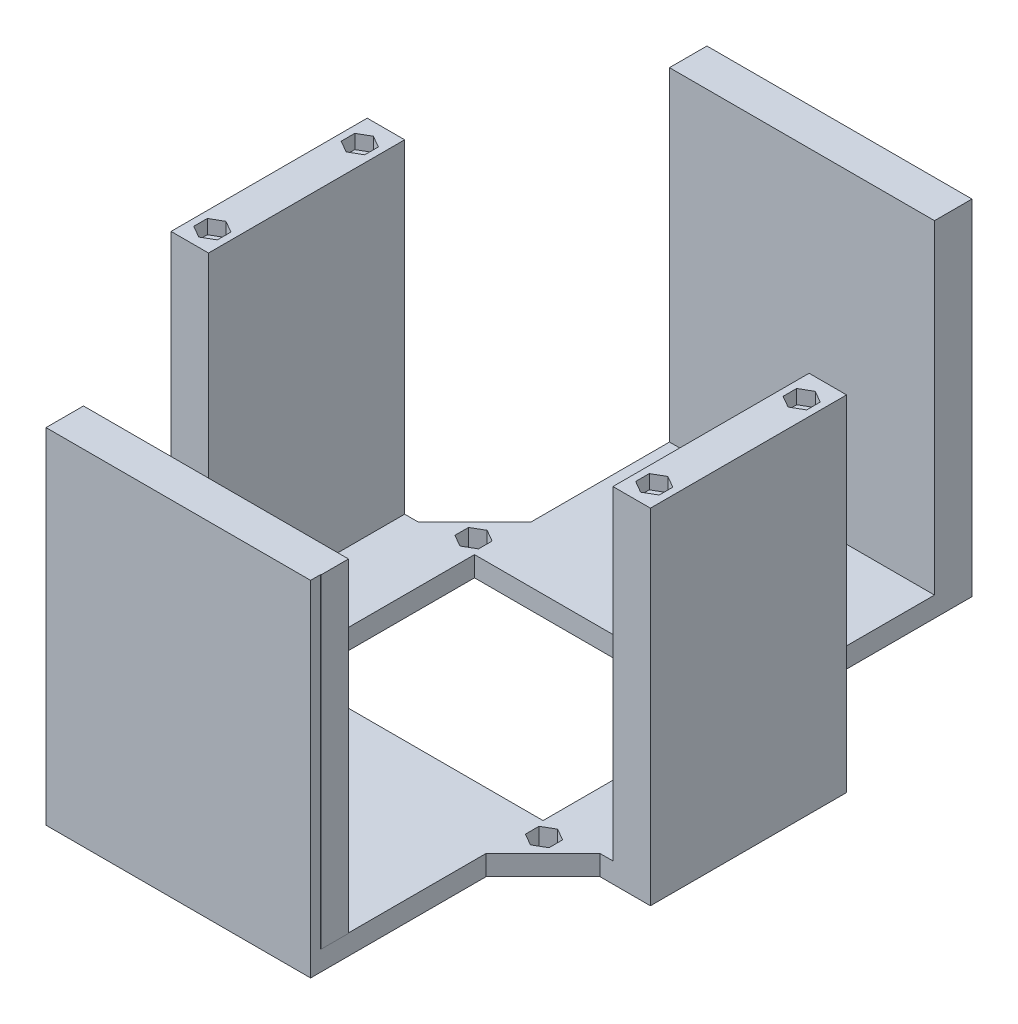
SolidWorks part; units mm, degrees
ref_plane "Front Plane" through (0, 0, 0) normal (0, 0, 1) x (1, 0, 0)
ref_plane "Top Plane" through (0, 0, 0) normal (0, 1, 0) x (1, 0, 0)
ref_plane "Right Plane" through (0, 0, 0) normal (1, 0, 0) x (0, 0, -1)
sketch "Sketch2" plane through (0, 0, 0) normal (0, 1, 0) x (1, 0, 0)
  line L0 (-32.8436, 36.3397) -> (-32.8436, 24.3397)
  line L1 (-32.8436, 24.3397) -> (-44.8436, 24.3397)
  line L2 (-44.8436, 24.3397) -> (-32.8436, 36.3397)
  line L3 (0, 57.5251) -> (0, -40.7887) construction
  line L4 (-92.2724, 0) -> (92.8059, 0) construction
  line L27 (32.8436, 24.3397) -> (44.8436, 24.3397)
  line L28 (32.8436, 36.3397) -> (32.8436, 24.3397)
  line L29 (44.8436, 24.3397) -> (32.8436, 36.3397)
  line L30 (44.8436, -24.3397) -> (32.8436, -36.3397)
  line L31 (32.8436, -36.3397) -> (32.8436, -24.3397)
  line L32 (32.8436, -24.3397) -> (44.8436, -24.3397)
  line L45 (-44.8436, -24.3397) -> (-32.8436, -36.3397)
  line L46 (-32.8436, -24.3397) -> (-44.8436, -24.3397)
  line L47 (-32.8436, -36.3397) -> (-32.8436, -24.3397)
  line L48 (39.425, -26.0613) -> (39.425, -29.4387)
  line L49 (-36.5, -31.1275) -> (-33.575, -29.4387)
  line L50 (-33.575, -29.4387) -> (-33.575, -26.0613)
  line L51 (-33.575, -26.0613) -> (-36.5, -24.3725)
  line L52 (-36.5, -24.3725) -> (-39.425, -26.0613)
  line L53 (-39.425, -26.0613) -> (-39.425, -29.4387)
  line L54 (-39.425, -29.4387) -> (-36.5, -31.1275)
  line L55 (39.425, -29.4387) -> (36.5, -31.1275)
  line L56 (36.5, -31.1275) -> (33.575, -29.4387)
  line L57 (33.575, -29.4387) -> (33.575, -26.0613)
  line L58 (33.575, -26.0613) -> (36.5, -24.3725)
  line L59 (36.5, -24.3725) -> (39.425, -26.0613)
  line L60 (33.575, 29.4387) -> (33.575, 26.0613)
  line L61 (36.5, 31.1275) -> (33.575, 29.4387)
  line L62 (39.425, 29.4387) -> (36.5, 31.1275)
  line L63 (39.425, 26.0613) -> (39.425, 29.4387)
  line L64 (36.5, 24.3725) -> (39.425, 26.0613)
  line L65 (33.575, 26.0613) -> (36.5, 24.3725)
  line L66 (-33.575, 29.4387) -> (-33.575, 26.0613)
  line L67 (-36.5, 31.1275) -> (-33.575, 29.4387)
  line L68 (-39.425, 29.4387) -> (-36.5, 31.1275)
  line L69 (-39.425, 26.0613) -> (-39.425, 29.4387)
  line L70 (-33.575, 26.0613) -> (-36.5, 24.3725)
  line L71 (-36.5, 24.3725) -> (-39.425, 26.0613)
  circle A7 centre (-36.5, -27.75) radius 2.925 construction
  point P0 (-36.5, 27.75)
  point P1 (-36.5, -27.75)
  point P2 (36.5, -27.75)
  point P3 (36.5, 27.75)
  point P43 (36.5, -27.75)
  point P55 (-36.5, -27.75)
  dimension "D6" = 12
  dimension "D2" = 73
  dimension "D3" = 55.5
  dimension "D8" = 73
  dimension "D9" = 55.5
  dimension "D10" = 27.75
  dimension "D11" = 5
  dimension "D12" = 36.5
  dimension "D13" = 36.5
  dimension "D5" = 12
  dimension "D14" = 27.75
  dimension "D15" = 27.75
  dimension "D16" = 5.85
extrude "Boss-Extrude1" add sketch "Sketch2" along normal blind 20
sketch "Sketch6" plane through (-32.8436, 0, 0) normal (1, 0, 0) x (0, 0, -1)
  line L0 (36.3397, 20) -> (36.3397, 0) construction
  line L1 (24.3397, 20) -> (36.3397, 20)
  line L2 (24.3397, 20) -> (24.3397, 15)
  line L3 (24.3397, 15) -> (36.3397, 15)
  line L4 (36.3397, 20) -> (36.3397, 15)
  line L5 (-24.3397, 20) -> (-24.3397, 0) construction
  line L6 (-36.3397, 20) -> (-24.3397, 20)
  line L7 (-36.3397, 20) -> (-36.3397, 15)
  line L8 (-36.3397, 15) -> (-24.3397, 15)
  line L9 (-24.3397, 20) -> (-24.3397, 15)
  dimension "D1" = 5
  dimension "D2" = 5
extrude "Boss-Extrude5" add sketch "Sketch6" along normal blind 65.8
sketch "Sketch7" plane through (0, 0, 24.3397) normal (0, 0, -1) x (-1, 0, 0)
  line L1 (-44.8436, 20) -> (-32.8436, 20)
  line L2 (-44.8436, 20) -> (-44.8436, 15)
  line L3 (-44.8436, 15) -> (-32.8436, 15)
  line L4 (-32.8436, 20) -> (-32.8436, 15)
  line L5 (32.8436, 15) -> (44.8436, 15)
  line L6 (32.8436, 15) -> (32.8436, 20)
  line L7 (32.8436, 20) -> (44.8436, 20)
  line L8 (44.8436, 15) -> (44.8436, 20)
extrude "Boss-Extrude6" add sketch "Sketch7" along normal blind 48.7
sketch "Sketch8" plane through (44.8436, 0, 0) normal (1, 0, 0) x (0, 0, -1)
  line L0 (24.3397, 15) -> (-24.3397, 15) construction
  line L1 (-24.3397, 20) -> (-12.1647, 20)
  line L2 (-24.3397, 20) -> (-24.3397, 15)
  line L3 (-24.3397, 15) -> (-12.1647, 15)
  line L4 (-12.1647, 20) -> (-12.1647, 15)
  line L5 (24.3603, 20) -> (-24.3397, 20) construction
  line L6 (24.3603, 15) -> (12.1853, 15)
  line L7 (24.3603, 15) -> (24.3603, 20)
  line L8 (24.3603, 20) -> (12.1853, 20)
  line L9 (12.1853, 15) -> (12.1853, 20)
  dimension "D1" = 12.175
  dimension "D2" = 12.175
extrude "Boss-Extrude7" add sketch "Sketch8" along normal blind 12.16
sketch "Sketch9" plane through (-44.8436, 0, 0) normal (-1, 0, 0) x (0, 0, 1)
  line L0 (-24.3397, 15) -> (24.3397, 15) construction
  line L1 (-24.3603, 20) -> (-12.1853, 20)
  line L2 (-24.3603, 20) -> (-24.3603, 15)
  line L3 (-24.3603, 15) -> (-12.1853, 15)
  line L4 (-12.1853, 20) -> (-12.1853, 15)
  line L5 (-24.3603, 20) -> (24.3397, 20) construction
  line L6 (24.3397, 15) -> (12.1647, 15)
  line L7 (24.3397, 15) -> (24.3397, 20)
  line L8 (24.3397, 20) -> (12.1647, 20)
  line L9 (12.1647, 15) -> (12.1647, 20)
  dimension "D1" = 12.175
  dimension "D2" = 12.175
extrude "Boss-Extrude8" add sketch "Sketch9" along normal blind 12.16
sketch "Sketch11" plane through (0, 20, 0) normal (0, 1, 0) x (1, 0, 0)
  line L0 (-57.0036, -24.3397) -> (-44.8436, -24.3397) construction
  line L1 (-50.2036, -24.3397) -> (-57.0036, -24.3397)
  line L2 (-50.2036, -24.3397) -> (-50.2036, -12.1647)
  line L3 (-50.2036, -12.1647) -> (-57.0036, -12.1647)
  line L4 (-57.0036, -24.3397) -> (-57.0036, -12.1647)
  line L5 (-57.0036, 12.1853) -> (-44.8436, 12.1853) construction
  line L6 (-57.0036, 24.3603) -> (-50.2036, 24.3603)
  line L7 (-57.0036, 24.3603) -> (-57.0036, 12.1853)
  line L8 (-57.0036, 12.1853) -> (-50.2036, 12.1853)
  line L9 (-50.2036, 24.3603) -> (-50.2036, 12.1853)
  line L10 (57.0036, 12.1853) -> (44.8436, 12.1853) construction
  line L11 (57.0036, 24.3603) -> (50.2036, 24.3603)
  line L12 (57.0036, 24.3603) -> (57.0036, 12.1853)
  line L13 (57.0036, 12.1853) -> (50.2036, 12.1853)
  line L14 (50.2036, 24.3603) -> (50.2036, 12.1853)
  line L15 (57.0036, -24.3397) -> (44.8436, -24.3397) construction
  line L16 (57.0036, -12.1647) -> (50.2036, -12.1647)
  line L17 (57.0036, -12.1647) -> (57.0036, -24.3397)
  line L18 (57.0036, -24.3397) -> (50.2036, -24.3397)
  line L19 (50.2036, -12.1647) -> (50.2036, -24.3397)
  dimension "D1" = 6.8
  dimension "D2" = 5.36
  dimension "D3" = 6.8
  dimension "D4" = 6.8
  dimension "D5" = 6.8
extrude "Boss-Extrude9" add sketch "Sketch11" along normal blind 80.5
sketch "Sketch14" plane through (0, 0, 36.3397) normal (0, 0, 1) x (1, 0, 0)
  line L0 (32.8436, 15) -> (-32.8436, 15) construction
  line L1 (-32.8436, 20) -> (-20.6686, 20)
  line L2 (-32.8436, 20) -> (-32.8436, 15)
  line L3 (-32.8436, 15) -> (-20.6686, 15)
  line L4 (-20.6686, 20) -> (-20.6686, 15)
  line L5 (32.9564, 20) -> (-32.8436, 20) construction
  line L6 (32.8436, 15) -> (20.6686, 15)
  line L7 (32.8436, 15) -> (32.8436, 20)
  line L8 (32.8436, 20) -> (20.6686, 20)
  line L9 (20.6686, 15) -> (20.6686, 20)
  dimension "D1" = 12.175
  dimension "D2" = 12.175
extrude "Boss-Extrude12" add sketch "Sketch14" along normal blind 43.2
sketch "Sketch15" plane through (0, 0, -36.3397) normal (0, 0, -1) x (-1, 0, 0)
  line L0 (-32.8436, 15) -> (32.8436, 15) construction
  line L1 (-32.9564, 20) -> (-20.7814, 20)
  line L2 (-32.9564, 20) -> (-32.9564, 15)
  line L3 (-32.9564, 15) -> (-20.7814, 15)
  line L4 (-20.7814, 20) -> (-20.7814, 15)
  line L6 (32.8436, 15) -> (20.6686, 15)
  line L7 (32.8436, 15) -> (32.8436, 20)
  line L8 (32.8436, 20) -> (20.6686, 20)
  line L9 (20.6686, 15) -> (20.6686, 20)
  dimension "D1" = 12.175
  dimension "D2" = 12.175
extrude "Boss-Extrude13" add sketch "Sketch15" along normal blind 43.2
sketch "Sketch16" plane through (0, 20, 0) normal (0, 1, 0) x (1, 0, 0)
  line L0 (-20.6686, 79.5397) -> (-20.6686, 36.3397) construction
  line L1 (-32.8436, 79.5397) -> (-20.6686, 79.5397)
  line L2 (-32.8436, 79.5397) -> (-32.8436, 72.7397)
  line L3 (-32.8436, 72.7397) -> (-20.6686, 72.7397)
  line L4 (-20.6686, 79.5397) -> (-20.6686, 72.7397)
  line L5 (32.9564, 79.5397) -> (32.9564, 36.2268) construction
  line L6 (20.7814, 79.5397) -> (32.9564, 79.5397)
  line L7 (20.7814, 79.5397) -> (20.7814, 72.7397)
  line L8 (20.7814, 72.7397) -> (32.9564, 72.7397)
  line L9 (32.9564, 79.5397) -> (32.9564, 72.7397)
  line L10 (-101.2794, 0) -> (102.0481, 0) construction
  line L11 (32.9564, -79.5397) -> (32.9564, -72.7397)
  line L12 (20.7814, -72.7397) -> (32.9564, -72.7397)
  line L13 (20.7814, -79.5397) -> (20.7814, -72.7397)
  line L14 (20.7814, -79.5397) -> (32.9564, -79.5397)
  line L15 (-20.6686, -79.5397) -> (-20.6686, -72.7397)
  line L16 (-32.8436, -72.7397) -> (-20.6686, -72.7397)
  line L17 (-32.8436, -79.5397) -> (-32.8436, -72.7397)
  line L18 (-32.8436, -79.5397) -> (-20.6686, -79.5397)
  dimension "D1" = 6.8
  dimension "D2" = 6.8
extrude "Boss-Extrude14" add sketch "Sketch16" along normal blind 80.5
sketch "Sketch17" plane through (34.5916, 0, -34.5916) normal (0.7071, 0, -0.7071) x (-0.7071, 0, -0.7071)
  line L1 (-14.4984, 15) -> (2.4721, 15)
  line L2 (-14.4984, 15) -> (-14.4984, 0)
  line L3 (-14.4984, 0) -> (2.4721, 0)
  line L4 (2.4721, 15) -> (2.4721, 0)
extrude "Cut-Extrude1" cut sketch "Sketch17" against normal blind 10
sketch "Sketch18" plane through (-34.5916, 0, -34.5916) normal (-0.7071, 0, -0.7071) x (-0.7071, 0, 0.7071)
  line L1 (-2.4721, 15) -> (14.4984, 15)
  line L2 (-2.4721, 15) -> (-2.4721, 0)
  line L3 (-2.4721, 0) -> (14.4984, 0)
  line L4 (14.4984, 15) -> (14.4984, 0)
extrude "Cut-Extrude2" cut sketch "Sketch18" against normal blind 10
sketch "Sketch19" plane through (-34.5916, 0, 34.5916) normal (-0.7071, 0, 0.7071) x (0.7071, 0, 0.7071)
  line L1 (-14.4984, 15) -> (2.4721, 15)
  line L2 (-14.4984, 15) -> (-14.4984, 0)
  line L3 (-14.4984, 0) -> (2.4721, 0)
  line L4 (2.4721, 15) -> (2.4721, 0)
extrude "Cut-Extrude3" cut sketch "Sketch19" against normal blind 10
sketch "Sketch20" plane through (34.5916, 0, 34.5916) normal (0.7071, 0, 0.7071) x (0.7071, 0, -0.7071)
  line L1 (-2.4721, 15) -> (14.4984, 15)
  line L2 (-2.4721, 15) -> (-2.4721, 0)
  line L3 (-2.4721, 0) -> (14.4984, 0)
  line L4 (14.4984, 15) -> (14.4984, 0)
extrude "Cut-Extrude4" cut sketch "Sketch20" against normal blind 10
sketch "Sketch21" plane through (-20.6686, 0, 0) normal (1, 0, 0) x (0, 0, -1)
  line L0 (-79.5397, 100.5) -> (-72.7397, 100.5)
  line L1 (-72.7397, 100.5) -> (-72.7397, 20)
  line L2 (-72.7397, 20) -> (-36.3397, 20)
  line L3 (-36.3397, 20) -> (-36.3397, 15)
  line L4 (-36.3397, 15) -> (-79.5397, 15)
  line L5 (-79.5397, 15) -> (-79.5397, 100.5)
  line L6 (79.5397, 100.5) -> (72.7397, 100.5)
  line L7 (72.7397, 100.5) -> (72.7397, 20)
  line L8 (72.7397, 20) -> (36.3397, 20)
  line L9 (36.3397, 20) -> (36.3397, 15)
  line L10 (36.3397, 15) -> (79.5397, 15)
  line L11 (79.5397, 15) -> (79.5397, 100.5)
extrude "Boss-Extrude15" add sketch "Sketch21" along normal blind 50
sketch "Sketch24" plane through (0, 20, 0) normal (0, 1, 0) x (1, 0, 0)
  line L0 (0, 83.7429) -> (0, -88.7492) construction
  circle A0 centre (-34.9978, 22.3503) radius 0.6971
  circle A1 centre (-34.9978, 13.9447) radius 0.7392
sketch "Sketch25" plane through (0, 0, -12.1853) normal (0, 0, 1) x (1, 0, 0)
  line L0 (-50.2036, 100.5) -> (-57.0036, 100.5)
  line L1 (-57.0036, 100.5) -> (-57.0036, 15)
  line L2 (-57.0036, 15) -> (-44.8436, 15)
  line L3 (-44.8436, 15) -> (-44.8436, 20)
  line L4 (-44.8436, 20) -> (-50.2036, 20)
  line L5 (-50.2036, 20) -> (-50.2036, 100.5)
  line L6 (50.2036, 100.5) -> (57.0036, 100.5)
  line L7 (57.0036, 100.5) -> (57.0036, 15)
  line L8 (57.0036, 15) -> (44.8436, 15)
  line L9 (44.8436, 15) -> (44.8436, 20)
  line L10 (44.8436, 20) -> (50.2036, 20)
  line L11 (50.2036, 20) -> (50.2036, 100.5)
extrude "Boss-Extrude16" add sketch "Sketch25" along normal blind 30
sketch "Sketch26" plane through (-34.5916, 0, 34.5916) normal (-0.7071, 0, 0.7071) x (0.7071, 0, 0.7071)
  line L1 (-14.4984, 20) -> (2.4721, 20)
  line L2 (-14.4984, 20) -> (-14.4984, 15)
  line L3 (-14.4984, 15) -> (2.4721, 15)
  line L4 (2.4721, 20) -> (2.4721, 15)
extrude "Boss-Extrude17" add sketch "Sketch26" along normal blind 1.5
sketch "Sketch27" plane through (1.7481, 0, 1.7481) normal (0.7071, 0, 0.7071) x (0.7071, 0, -0.7071)
  line L1 (-50.4199, 20) -> (-48.9199, 20)
  line L2 (-50.4199, 20) -> (-50.4199, 15)
  line L3 (-50.4199, 15) -> (-48.9199, 15)
  line L4 (-48.9199, 20) -> (-48.9199, 15)
extrude "Boss-Extrude18" add sketch "Sketch27" along normal blind 2.5
sketch "Sketch28" plane through (-10.2519, 0, -10.2519) normal (-0.7071, 0, -0.7071) x (-0.7071, 0, 0.7071)
  line L1 (50.4199, 20) -> (48.9199, 20)
  line L2 (50.4199, 20) -> (50.4199, 15)
  line L3 (50.4199, 15) -> (48.9199, 15)
  line L4 (48.9199, 20) -> (48.9199, 15)
extrude "Boss-Extrude20" add sketch "Sketch28" along normal blind 2.5
sketch "Sketch29" plane through (34.5916, 0, 34.5916) normal (0.7071, 0, 0.7071) x (0.7071, 0, -0.7071)
  line L0 (14.4984, 15) -> (-2.3125, 15) construction
  line L1 (14.4984, 20) -> (-2.3125, 20)
  line L2 (14.4984, 20) -> (14.4984, 15)
  line L3 (14.4984, 15) -> (-2.3125, 15)
  line L4 (-2.3125, 20) -> (-2.3125, 15)
extrude "Boss-Extrude21" add sketch "Sketch29" along normal blind 1.5
sketch "Sketch30" plane through (-1.6352, 0, 1.6352) normal (-0.7071, 0, 0.7071) x (0.7071, 0, 0.7071)
  line L1 (50.4199, 20) -> (48.9199, 20)
  line L2 (50.4199, 20) -> (50.4199, 15)
  line L3 (50.4199, 15) -> (48.9199, 15)
  line L4 (48.9199, 20) -> (48.9199, 15)
extrude "Boss-Extrude22" add sketch "Sketch30" along normal blind 3.5
sketch "Sketch31" plane through (10.2519, 0, -10.2519) normal (0.7071, 0, -0.7071) x (-0.7071, 0, -0.7071)
  line L1 (-50.4199, 20) -> (-48.9199, 20)
  line L2 (-50.4199, 20) -> (-50.4199, 15)
  line L3 (-50.4199, 15) -> (-48.9199, 15)
  line L4 (-48.9199, 20) -> (-48.9199, 15)
extrude "Boss-Extrude23" add sketch "Sketch31" along normal blind 3.5
sketch "Sketch32" plane through (34.5916, 0, -34.5916) normal (0.7071, 0, -0.7071) x (-0.7071, 0, -0.7071)
  line L1 (-14.4692, 20) -> (2.3125, 20)
  line L2 (-14.4692, 20) -> (-14.4692, 15)
  line L3 (-14.4692, 15) -> (2.3125, 15)
  line L4 (2.3125, 20) -> (2.3125, 15)
extrude "Boss-Extrude24" add sketch "Sketch32" along normal blind 1.5
sketch "Sketch33" plane through (10.2313, 0, 10.2313) normal (0.7071, 0, 0.7071) x (0.7071, 0, -0.7071)
  line L1 (50.4199, 20) -> (48.9199, 20)
  line L2 (50.4199, 20) -> (50.4199, 15)
  line L3 (50.4199, 15) -> (48.9199, 15)
  line L4 (48.9199, 20) -> (48.9199, 15)
extrude "Boss-Extrude25" add sketch "Sketch33" along normal blind 2.5
sketch "Sketch34" plane through (-1.6352, 0, -1.6352) normal (-0.7071, 0, -0.7071) x (-0.7071, 0, 0.7071)
  line L1 (-50.4199, 20) -> (-48.9199, 20)
  line L2 (-50.4199, 20) -> (-50.4199, 15)
  line L3 (-50.4199, 15) -> (-48.9199, 15)
  line L4 (-48.9199, 20) -> (-48.9199, 15)
extrude "Boss-Extrude26" add sketch "Sketch34" along normal blind 2.5
sketch "Sketch35" plane through (-34.5916, 0, -34.5916) normal (-0.7071, 0, -0.7071) x (-0.7071, 0, 0.7071)
  line L1 (-2.4721, 20) -> (14.4692, 20)
  line L2 (-2.4721, 20) -> (-2.4721, 15)
  line L3 (-2.4721, 15) -> (14.4692, 15)
  line L4 (14.4692, 20) -> (14.4692, 15)
extrude "Boss-Extrude27" add sketch "Sketch35" along normal blind 1.5
sketch "Sketch36" plane through (1.7481, 0, -1.7481) normal (0.7071, 0, -0.7071) x (-0.7071, 0, -0.7071)
  line L1 (48.9199, 20) -> (50.4199, 20)
  line L2 (48.9199, 20) -> (48.9199, 15)
  line L3 (48.9199, 15) -> (50.4199, 15)
  line L4 (50.4199, 20) -> (50.4199, 15)
extrude "Boss-Extrude28" add sketch "Sketch36" along normal blind 2.5
sketch "Sketch38" plane through (-10.2313, 0, 10.2313) normal (-0.7071, 0, 0.7071) x (0.7071, 0, 0.7071)
  line L1 (-50.4199, 20) -> (-48.9199, 20)
  line L2 (-50.4199, 20) -> (-50.4199, 15)
  line L3 (-50.4199, 15) -> (-48.9199, 15)
  line L4 (-48.9199, 20) -> (-48.9199, 15)
extrude "Boss-Extrude29" add sketch "Sketch38" along normal blind 2.5
sketch "Sketch43" plane through (-57.0036, 0, 0) normal (-1, 0, 0) x (0, 0, 1)
  line L1 (-24.3603, 100.5) -> (24.3397, 100.5)
  line L2 (-24.3603, 100.5) -> (-24.3603, 15)
  line L3 (-24.3603, 15) -> (24.3397, 15)
  line L4 (24.3397, 100.5) -> (24.3397, 15)
extrude "Boss-Extrude30" add sketch "Sketch43" along normal blind 2.5
sketch "Sketch44" plane through (57.0036, 0, 0) normal (1, 0, 0) x (0, 0, -1)
  line L1 (-24.3397, 100.5) -> (24.3603, 100.5)
  line L2 (-24.3397, 100.5) -> (-24.3397, 15)
  line L3 (-24.3397, 15) -> (24.3603, 15)
  line L4 (24.3603, 100.5) -> (24.3603, 15)
extrude "Boss-Extrude31" add sketch "Sketch44" along normal blind 2.5
sketch "Sketch45" plane through (0, 0, 79.5397) normal (0, 0, 1) x (1, 0, 0)
  line L1 (-32.8436, 100.5) -> (32.8436, 100.5)
  line L2 (-32.8436, 100.5) -> (-32.8436, 15)
  line L3 (-32.8436, 15) -> (32.8436, 15)
  line L4 (32.8436, 100.5) -> (32.8436, 15)
extrude "Boss-Extrude32" add sketch "Sketch45" along normal blind 2.5
sketch "Sketch46" plane through (0, 0, -79.5397) normal (0, 0, -1) x (-1, 0, 0)
  line L1 (-32.9564, 100.5) -> (32.8436, 100.5)
  line L2 (-32.9564, 100.5) -> (-32.9564, 15)
  line L3 (-32.9564, 15) -> (32.8436, 15)
  line L4 (32.8436, 100.5) -> (32.8436, 15)
extrude "Boss-Extrude33" add sketch "Sketch46" along normal blind 2.5
sketch "Sketch47" plane through (0, 100.5, 0) normal (0, 1, 0) x (1, 0, 0)
  line L1 (-54.8536, -22.1168) -> (-51.9286, -20.4281)
  line L2 (-51.9286, -20.4281) -> (-51.9286, -17.0506)
  line L3 (-51.9286, -17.0506) -> (-54.8536, -15.3618)
  line L4 (-54.8536, -15.3618) -> (-57.7786, -17.0506)
  line L5 (-57.7786, -17.0506) -> (-57.7786, -20.4281)
  line L6 (-57.7786, -20.4281) -> (-54.8536, -22.1168)
  line L8 (57.7786, 16.1716) -> (54.8536, 14.4828)
  line L9 (57.7786, 19.5491) -> (57.7786, 16.1716)
  line L10 (-50.2036, -24.3397) -> (-50.2036, 24.3603) construction
  line L11 (-50.2036, 24.3603) -> (-59.5036, 24.3603) construction
  line L12 (-54.8536, 14.4828) -> (-51.9286, 16.1716)
  line L13 (-51.9286, 16.1716) -> (-51.9286, 19.5491)
  line L14 (-51.9286, 19.5491) -> (-54.8536, 21.2378)
  line L15 (-54.8536, 21.2378) -> (-57.7786, 19.5491)
  line L16 (-57.7786, 19.5491) -> (-57.7786, 16.1716)
  line L17 (-57.7786, 16.1716) -> (-54.8536, 14.4828)
  line L18 (-59.5036, -24.3397) -> (-50.2036, -24.3397) construction
  line L19 (54.8536, 21.2378) -> (57.7786, 19.5491)
  line L20 (51.9286, 19.5491) -> (54.8536, 21.2378)
  line L21 (51.9286, 16.1716) -> (51.9286, 19.5491)
  line L22 (54.8536, 14.4828) -> (51.9286, 16.1716)
  line L23 (57.7786, -20.4281) -> (54.8536, -22.1168)
  line L24 (57.7786, -17.0506) -> (57.7786, -20.4281)
  line L25 (54.8536, -15.3618) -> (57.7786, -17.0506)
  line L26 (51.9286, -17.0506) -> (54.8536, -15.3618)
  line L27 (51.9286, -20.4281) -> (51.9286, -17.0506)
  line L28 (54.8536, -22.1168) -> (51.9286, -20.4281)
  circle A0 centre (-54.8536, -18.7393) radius 2.925 construction
  circle A1 centre (-54.8536, 17.8603) radius 2.925 construction
  circle A2 centre (54.8536, 17.8603) radius 2.925 construction
  circle A3 centre (54.8536, -18.7393) radius 2.925 construction
  dimension "D1" = 5.85
  dimension "D2" = 4.65
  dimension "D3" = 5.85
  dimension "D4" = 4.65
  dimension "D5" = 6.5
  dimension "D6" = 5.6003
extrude "Cut-Extrude5" cut sketch "Sketch47" against normal blind 3.5
